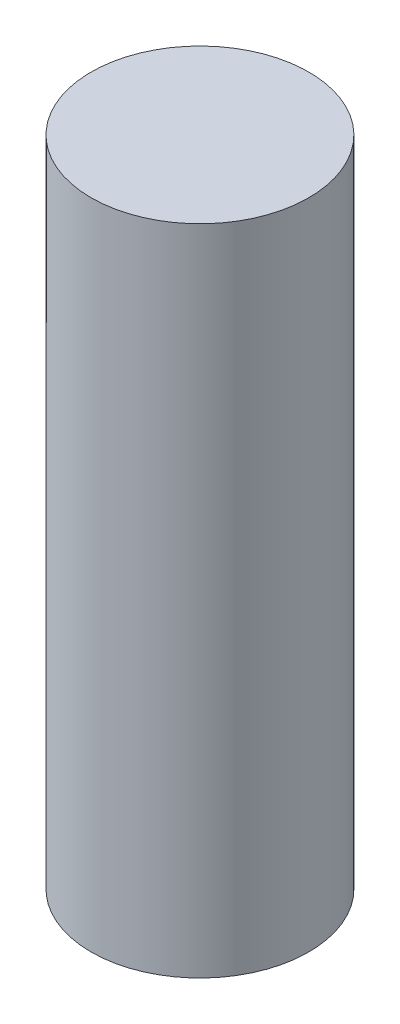
SolidWorks part; units mm, degrees
ref_plane "Front Plane" through (0, 0, 0) normal (0, 0, 1) x (1, 0, 0)
ref_plane "Top Plane" through (0, 0, 0) normal (0, 1, 0) x (1, 0, 0)
ref_plane "Right Plane" through (0, 0, 0) normal (1, 0, 0) x (0, 0, -1)
sketch "Sketch1" plane through (0, 0, 0) normal (0, 1, 0) x (1, 0, 0)
  circle A0 centre (0, 0) radius 5
  dimension "D1" = 10
extrude "Boss-Extrude1" add sketch "Sketch1" along normal blind 30
